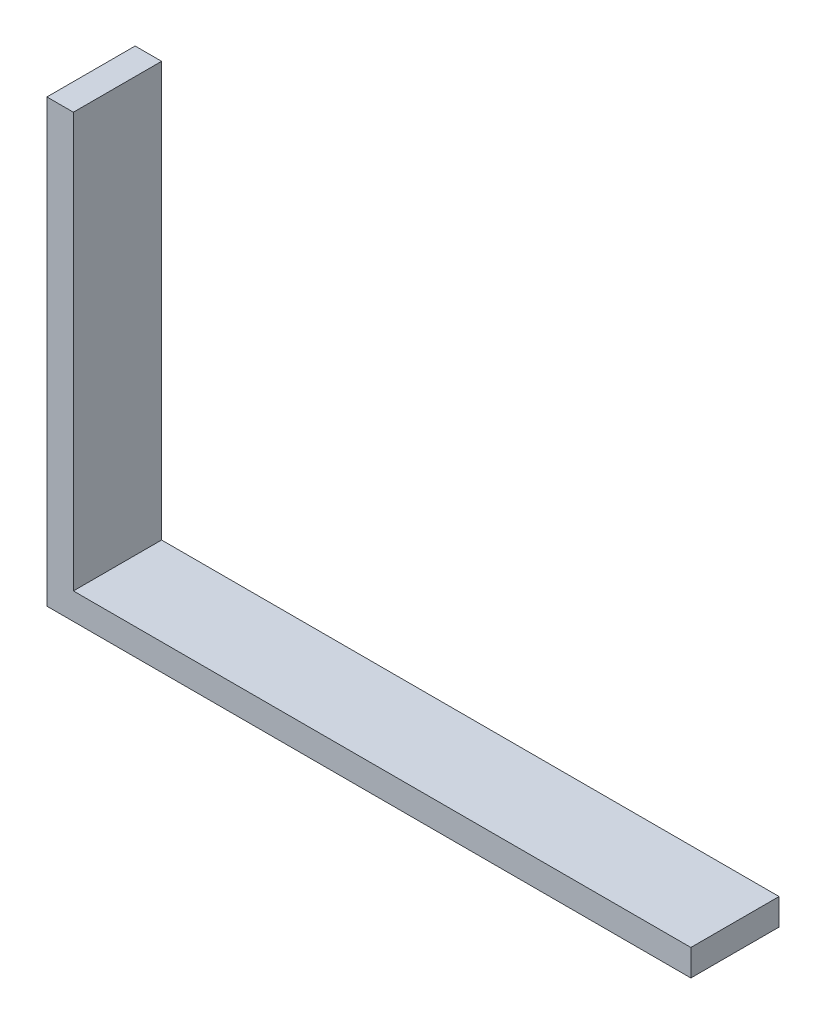
SolidWorks part; units mm, degrees
ref_plane "Front Plane" through (0, 0, 0) normal (0, 0, 1) x (1, 0, 0)
ref_plane "Top Plane" through (0, 0, 0) normal (0, 1, 0) x (1, 0, 0)
ref_plane "Right Plane" through (0, 0, 0) normal (1, 0, 0) x (0, 0, -1)
sketch "Sketch1" plane through (0, 0, 0) normal (0, 0, 1) x (1, 0, 0)
  line L0 (0, 0) -> (0, 50)
  line L1 (0, 50) -> (3, 50)
  line L2 (3, 50) -> (3, 3)
  line L3 (3, 3) -> (73, 3)
  line L4 (73, 3) -> (73, 0)
  line L5 (73, 0) -> (0, 0)
  dimension "D1" = 50
  dimension "D2" = 3
  dimension "D3" = 3
  dimension "D4" = 70
extrude "Boss-Extrude1" add sketch "Sketch1" along normal blind 10
